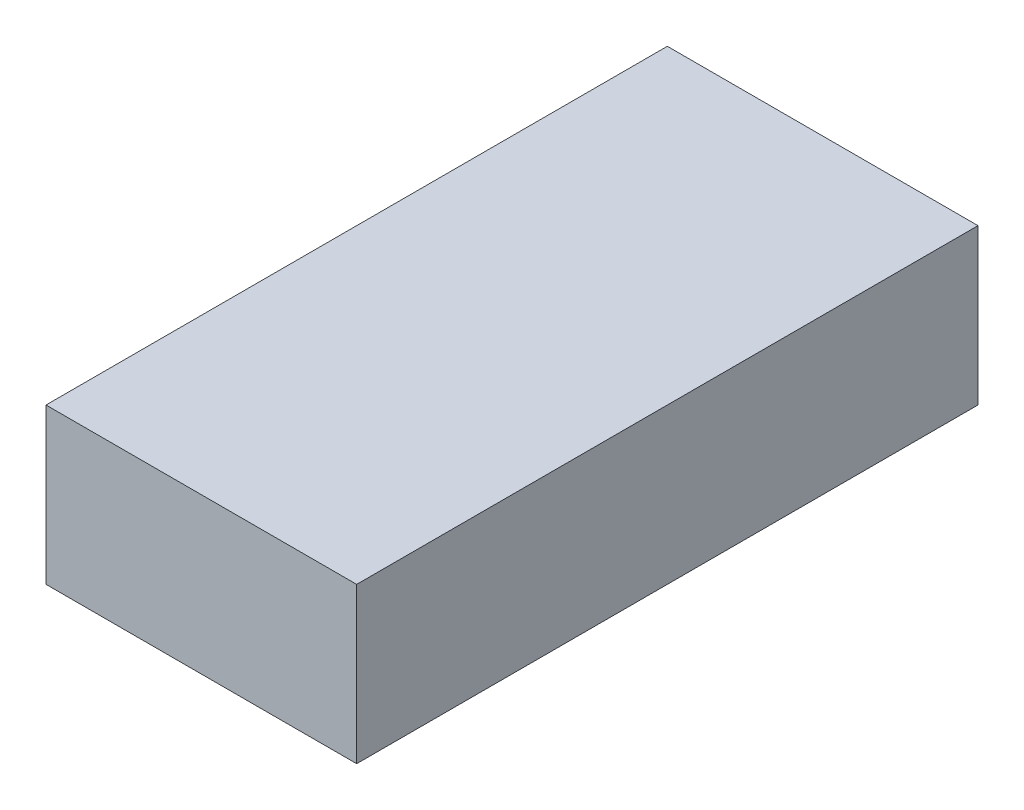
SolidWorks part; units mm, degrees
ref_plane "Front Plane" through (0, 0, 0) normal (0, 0, 1) x (1, 0, 0)
ref_plane "Top Plane" through (0, 0, 0) normal (0, 1, 0) x (1, 0, 0)
ref_plane "Right Plane" through (0, 0, 0) normal (1, 0, 0) x (0, 0, -1)
sketch "Sketch1" plane through (0, 0, 0) normal (0, 1, 0) x (1, 0, 0)
  line L1 (0, 0) -> (304.8, 0)
  line L2 (0, 0) -> (0, 609.6)
  line L3 (0, 609.6) -> (304.8, 609.6)
  line L4 (304.8, 0) -> (304.8, 609.6)
  dimension "D1" = 609.6
  dimension "D2" = 304.8
extrude "Boss-Extrude1" add sketch "Sketch1" along normal blind 152.4
